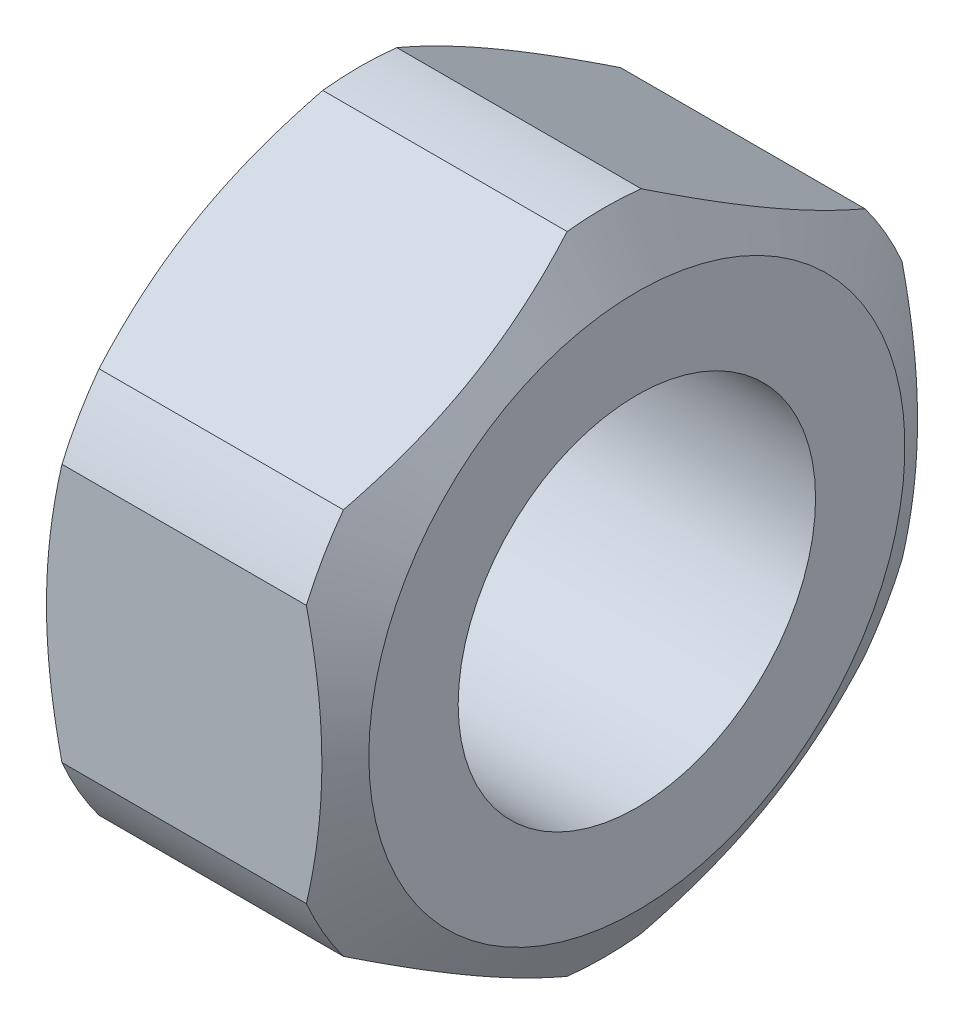
SolidWorks part; units mm, degrees
material "AISI 1020"
ref_plane "Спереди" through (0, 0, 0) normal (0, 0, 1) x (1, 0, 0)
ref_plane "Сверху" through (0, 0, 0) normal (0, 1, 0) x (1, 0, 0)
ref_plane "Справа" through (0, 0, 0) normal (1, 0, 0) x (0, 0, -1)
sketch "Эскиз1" plane through (0, 0, 0) normal (0, 0, 1) x (1, 0, 0)
  line L0 (-345.3781, 0) -> (16923.5283, 0) construction
  line L1 (0, -345.3781) -> (0, 16923.5283) construction
  line L2 (2.6, 3) -> (-2.6, 3)
  line L3 (-2.6, 3) -> (-2.6, 4.5)
  line L4 (-2.6, 4.5) -> (-2.0515, 5.45)
  line L5 (-2.0515, 5.45) -> (2.0515, 5.45)
  line L6 (2.6, 3) -> (2.6, 4.5)
  line L7 (2.6, 4.5) -> (2.0515, 5.45)
  point P11 (0, 3)
  point P13 (0, 5.45)
  dimension "D1" = 30
  dimension "d" = 6
  dimension "m" = 5.2
  dimension "e" = 10.9
  dimension "dw" = 9
revolve "Повернуть1" add sketch "Эскиз1" angle 360 about L0
sketch "Эскиз2" plane through (-2.6, 0, 0) normal (-1, 0, 0) x (0, 0, 1)
  line L1 (0, -5.7735) -> (5, -2.8868)
  line L2 (5, -2.8868) -> (5, 2.8868)
  line L3 (5, 2.8868) -> (0, 5.7735)
  line L4 (0, 5.7735) -> (-5, 2.8868)
  line L5 (-5, 2.8868) -> (-5, -2.8868)
  line L6 (-5, -2.8868) -> (0, -5.7735)
  circle A0 centre (0, 0) radius 5 construction
  dimension "D1" = 10
extrude "Вырез-Вытянуть1" cut sketch "Эскиз2" against normal through all flip side to cut
